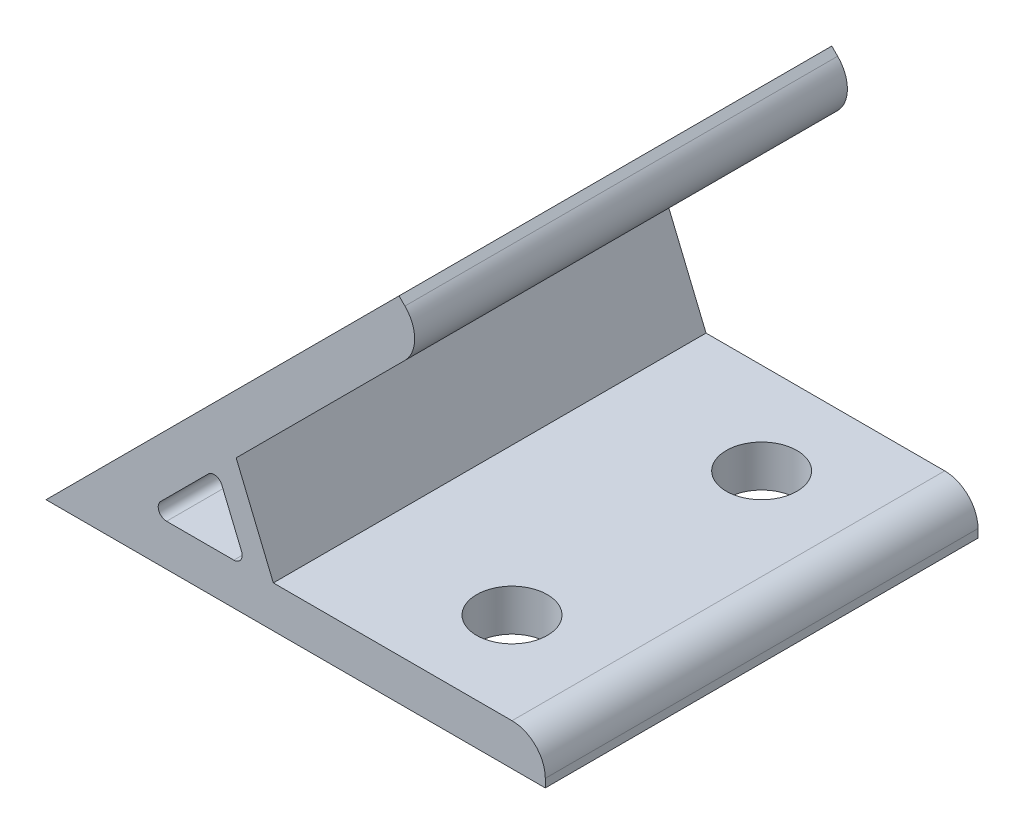
SolidWorks part; units mm, degrees
material "6063 T5"
ref_plane "Спереди" through (0, 0, 0) normal (0, 0, 1) x (1, 0, 0)
ref_plane "Сверху" through (0, 0, 0) normal (0, 1, 0) x (1, 0, 0)
ref_plane "Справа" through (0, 0, 0) normal (1, 0, 0) x (0, 0, -1)
sketch "Эскиз1" plane through (0, 0, 0) normal (0, 0, 1) x (1, 0, 0)
  line L0 (0, 0) -> (42.4264, 42.4264)
  line L1 (42.4264, 42.4264) -> (45.9619, 38.8909)
  line L2 (45.9619, 38.8909) -> (22.8524, 15.7814)
  line L3 (22.8524, 15.7814) -> (27.3182, 5)
  line L4 (27.3182, 5) -> (60, 5)
  line L5 (60, 5) -> (60, 0)
  line L6 (60, 0) -> (0, 0)
  line L7 (20.5563, 13.4853) -> (24.0711, 5)
  line L8 (24.0711, 5) -> (12.0711, 5)
  line L9 (12.0711, 5) -> (20.5563, 13.4853)
  line L10 (18.0711, 5) -> (18.0711, 0) construction
  line L11 (16.3137, 9.2426) -> (12.7782, 12.7782) construction
  line L12 (0, 0) -> (22.3137, 9.2426) construction
  dimension "D1" = 60
  dimension "D2" = 45
  dimension "D4" = 5
  dimension "D5" = 3
  dimension "D6" = 12
extrude "Бобышка-Вытянуть1" add sketch "Эскиз1" along normal mid plane 52
sketch "Эскиз2" plane through (0, 0, 0) normal (-0.7071, 0.7071, 0) x (0, 0, 1)
  line L0 (26, 60) -> (-26, 60) construction
  line L1 (-15, 45) -> (15, 45) construction
  line L2 (-26, 60) -> (-26, 0) construction
  circle A0 centre (-15, 45) radius 4.25
  circle A1 centre (15, 45) radius 4.25
  point P2 (0, 45)
  dimension "D1" = 8.5
  dimension "D2" = 15
  dimension "D4" = 11
  dimension "D3" = 30
extrude "Вырез-Вытянуть1" cut sketch "Эскиз2" against normal up to surface (5 mm away) up to face at (34.4072, 27.3361, 0)
sketch "Эскиз3" plane through (0, 0, 0) normal (0, -1, 0) x (1, 0, 0)
  line L0 (60, 26) -> (60, -26) construction
  line L1 (45, 15) -> (45, -15) construction
  circle A0 centre (45, 15) radius 4.25
  circle A1 centre (45, -15) radius 4.25
  point P2 (45, 0)
  dimension "D1" = 8.5
  dimension "D2" = 15
  dimension "D3" = 30
extrude "Вырез-Вытянуть2" cut sketch "Эскиз3" against normal up to surface (5 mm away) up to face at (43.6591, 5, 0)
fillet "Скругление1" radius 4 2 edges at (60, 5, 0) (45.9619, 38.8909, 0)
fillet "Скругление2" radius 1 3 edges at (20.5563, 13.4853, 0) (12.0711, 5, 0) (24.0711, 5, 0)
